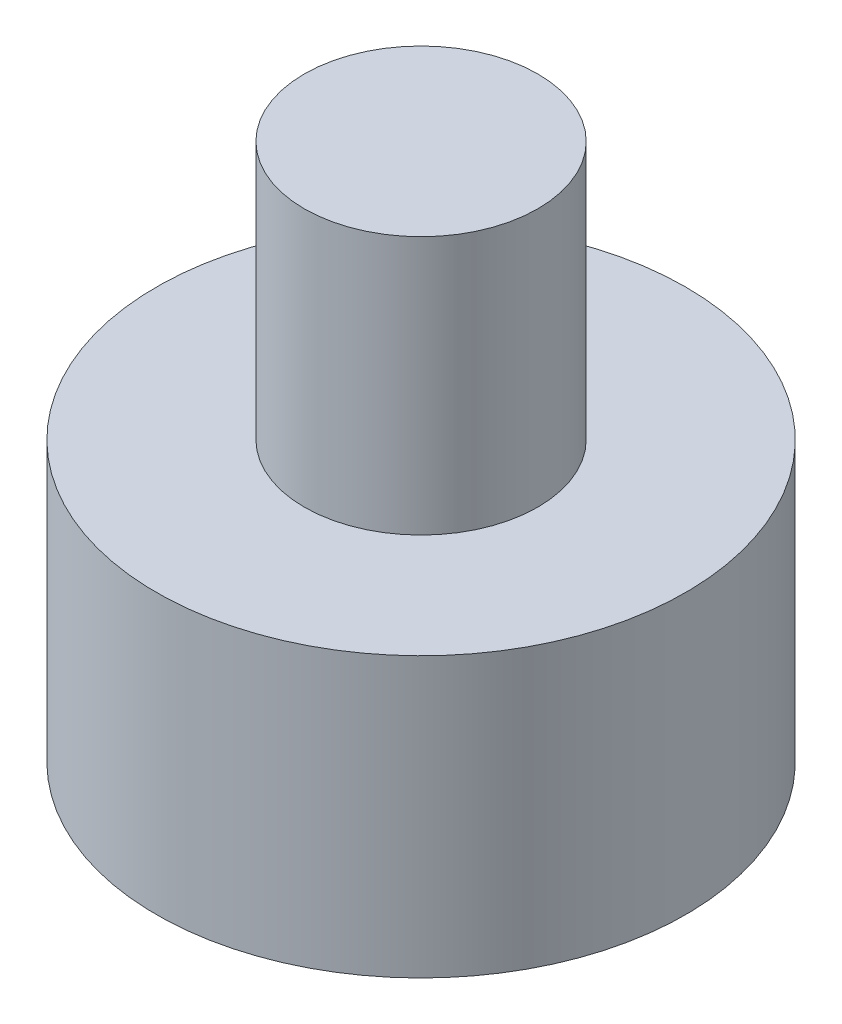
SolidWorks part; units mm, degrees
ref_plane "정면" through (0, 0, 0) normal (0, 0, 1) x (1, 0, 0)
ref_plane "윗면" through (0, 0, 0) normal (0, 1, 0) x (1, 0, 0)
ref_plane "우측면" through (0, 0, 0) normal (1, 0, 0) x (0, 0, -1)
sketch "스케치1" plane through (0, 0, 0) normal (0, 0, 1) x (1, 0, 0)
  line L0 (0, 17.8796) -> (0, 119.8492)
  line L1 (0, 17.8796) -> (0, 119.8492) construction
  line L2 (0, 119.8492) -> (22.1588, 119.8492)
  line L3 (22.1588, 119.8492) -> (22.1588, 70.8253)
  line L4 (22.1588, 70.8253) -> (50.2005, 70.8253)
  line L5 (50.2005, 70.8253) -> (50.2005, 17.8796)
  line L6 (50.2005, 17.8796) -> (0, 17.8796)
  line L7 (0, 17.8796) -> (0, 119.8492) construction
  point P2 (10, 119.8492)
  dimension "D1" = 22.1588
  dimension "D2" = 49.0239
  dimension "D3" = 52.9458
  dimension "D4" = 50.2005
  dimension "D5" = 0
revolve "회전3" add sketch "스케치1" angle 360 about L1
